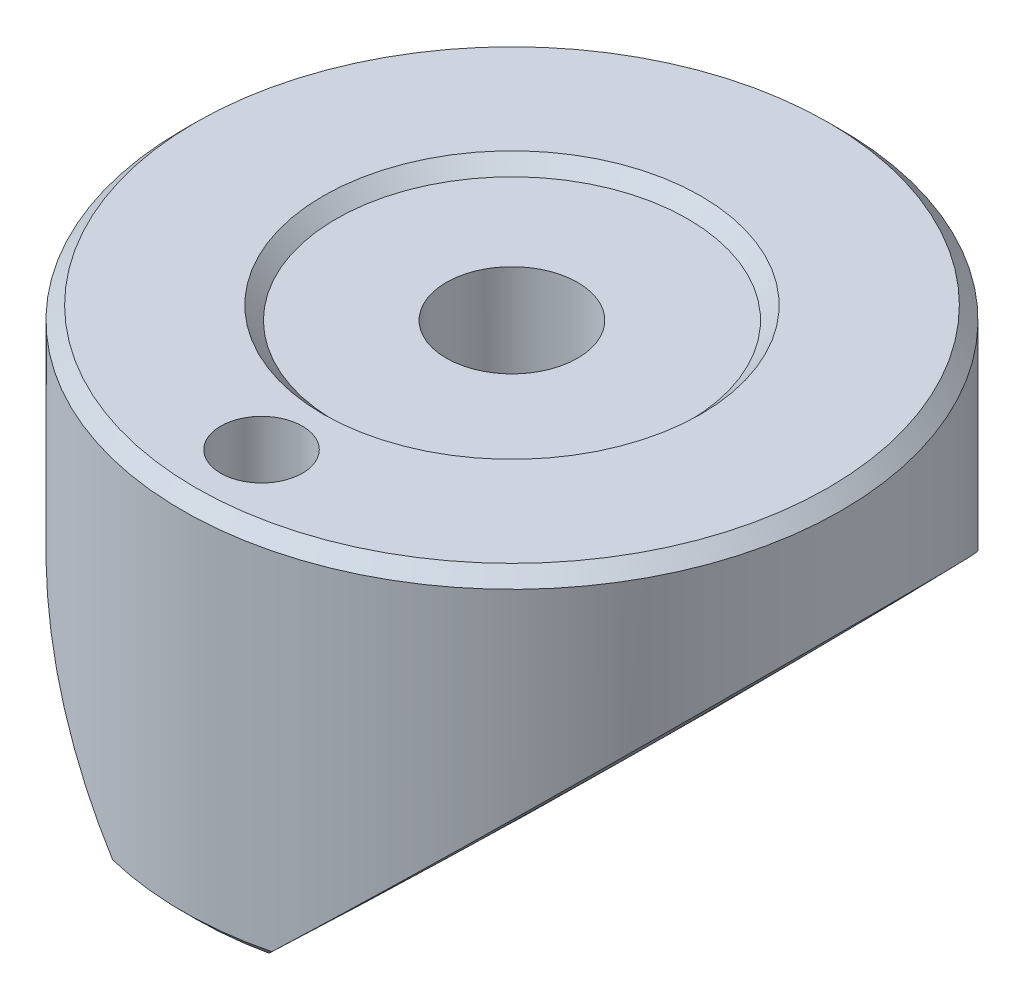
SolidWorks part; units mm, degrees
material "440C Rc 58"
ref_plane "Front Plane" through (0, 0, 0) normal (0, 0, 1) x (1, 0, 0)
ref_plane "Top Plane" through (0, 0, 0) normal (0, 1, 0) x (1, 0, 0)
ref_plane "Right Plane" through (0, 0, 0) normal (1, 0, 0) x (0, 0, -1)
sketch "V-surface mate" plane through (0, 0, 0) normal (0, 0, 1) x (1, 0, 0)
  line L0 (9.525, 15.9923) -> (-9.525, 15.9923) construction
  line L1 (-9.525, 15.9923) -> (-9.525, 13.0133) construction
  line L2 (-9.525, 13.0133) -> (-1.5917, 5.08) construction
  line L3 (-1.5917, 5.08) -> (1.5917, 5.08) construction
  line L4 (1.5917, 5.08) -> (9.525, 13.0133) construction
  line L5 (9.525, 15.9923) -> (9.525, 13.0133) construction
  line L6 (9.525, 15.9923) -> (-9.525, 15.9923) construction
  line L7 (-9.525, 15.9923) -> (-9.525, 13.0133) construction
  line L8 (-9.525, 13.0133) -> (-1.5917, 5.08) construction
  line L9 (-1.5917, 5.08) -> (1.5917, 5.08) construction
  line L10 (1.5917, 5.08) -> (9.525, 13.0133) construction
  line L11 (9.525, 15.9923) -> (9.525, 13.0133) construction
  line L12 (-2.8617, 6.35) -> (2.8617, 6.35) construction
  line L13 (7.0527, 10.541) -> (9.525, 10.541) construction
  line L14 (9.525, 10.541) -> (9.525, 13.0133) construction
  line L15 (-7.0527, 10.541) -> (-9.525, 10.541) construction
  line L16 (-9.525, 10.541) -> (-9.525, 13.0133) construction
  dimension "D1" = 1.27
sketch "Sketch3" plane through (0, 0, 0) normal (0, 0, 1) x (1, 0, 0)
  line L0 (0, 5.715) -> (-9.525, 5.715)
  line L1 (0, 16.51) -> (0, 5.715)
  line L3 (-1.5917, 5.08) -> (1.5917, 5.08) construction
  line L4 (0, 5.715) -> (0, 16.51) construction
  line L6 (-9.525, 5.715) -> (-9.525, 16.51)
  line L7 (-9.525, 16.51) -> (0, 16.51)
  dimension "D1" = 0.635
  dimension "D2" = 16.51
  dimension "D3" = 9.525
revolve "Revolve1" add sketch "Sketch3" angle 360 about L4
sketch "Sketch10" plane through (0, 0, 0) normal (0, 1, 0) x (1, 0, 0)
  circle A0 centre (0, -7.239) radius 1.1811
  dimension "D1" = 2.3622
  dimension "D2" = 7.239
extrude "Cut-Extrude1" cut sketch "Sketch10" along normal through all
chamfer "Chamfer1" distance 0.381 angle 45 2 edges at (9.525, 5.715, 0) (9.525, 16.51, 0)
hole_wizard "#10-24 Tapped Hole1" positions "Sketch14" profile "Sketch13" tap size "#10-24" standard "ANSI Inch"
sketch "Sketch14" plane through (0, 16.51, 0) normal (0, 1, 0) x (1, 0, 0)
  point P0 (0, 0)
sketch "Sketch13" plane through (0, 16.51, 0) normal (1, 0, 0) x (0, 0, 1)
  line L0 (0, 0) -> (0, 7.4908)
  line L1 (0, 7.4908) -> (1.8986, 6.35)
  line L2 (1.8986, 6.35) -> (1.8986, 0)
  line L5 (1.8986, 0) -> (0, 0)
  line L10 (0, 7.4908) -> (-1.8987, 6.35) construction
  line L11 (0, -6.35) -> (0, 107.95) construction
  dimension "Tap Drill Dia." = 3.7973
  dimension "Tap Drill Depth" = 6.35
  dimension "Drill Angle" = 118
cosmetic thread "Hole Thread1" parameters "D1"=5.08, "D2"=4.826
sketch "Sketch15" plane through (0, 0, 0) normal (0, 0, 1) x (1, 0, 0)
  line L1 (-9.525, 13.0133) -> (-1.5917, 5.08) construction
  line L2 (-9.144, 5.715) -> (9.144, 5.715) construction
  line L3 (-2.2267, 5.715) -> (-9.525, 13.0133) construction
  line L4 (-5.8758, 9.3642) -> (170.9095, 186.1495) construction
  line L5 (-11.5788, 15.2574) -> (-11.5788, 2.5363)
  line L6 (-11.5788, 2.5363) -> (1.2265, 2.5363)
  line L7 (170.9095, 186.1495) -> (170.9095, 31.0966) construction
  arc A0 (1.2265, 2.5363) -> (-11.5788, 15.2574) centre (170.9095, 186.1495) cw
  point P5 (-2.2267, 5.715)
  dimension "D1" = 250.0122
  dimension "D2" = 250.0122
revolve "Cut-Revolve3" cut sketch "Sketch15" angle 360 about L7
mirror "Mirror2" about plane through (0, 0, 0) normal (1, 0, 0) of "Cut-Revolve3"
sketch "Sketch16" plane through (0, 0, 0) normal (0, 0, 1) x (1, 0, 0)
  line L0 (0, 0) -> (0, 20.1707) construction
  line L1 (0, 16.9992) -> (0, 16.129)
  line L2 (0, 16.129) -> (5.08, 16.129)
  line L3 (5.08, 16.129) -> (6.3409, 17.3899)
  line L4 (6.3409, 17.3899) -> (0, 16.9992)
  line L5 (9.144, 16.51) -> (-9.144, 16.51) construction
  dimension "D1" = 0.381
  dimension "D2" = 5.08
revolve "Cut-Revolve4" cut sketch "Sketch16" angle 360 about L0
ref_plane "Plane1" through (0, 10.668, 0) normal (0, 1, 0) x (1, 0, 0)
sketch "Sketch17" plane through (0, 10.668, 0) normal (0, 1, 0) x (1, 0, 0)
  line L0 (0, 0) -> (50000, 0) construction
  line L1 (7.1797, -5.6626) -> (7.1797, 5.6626) construction
  point P3 (7.1797, 0)
